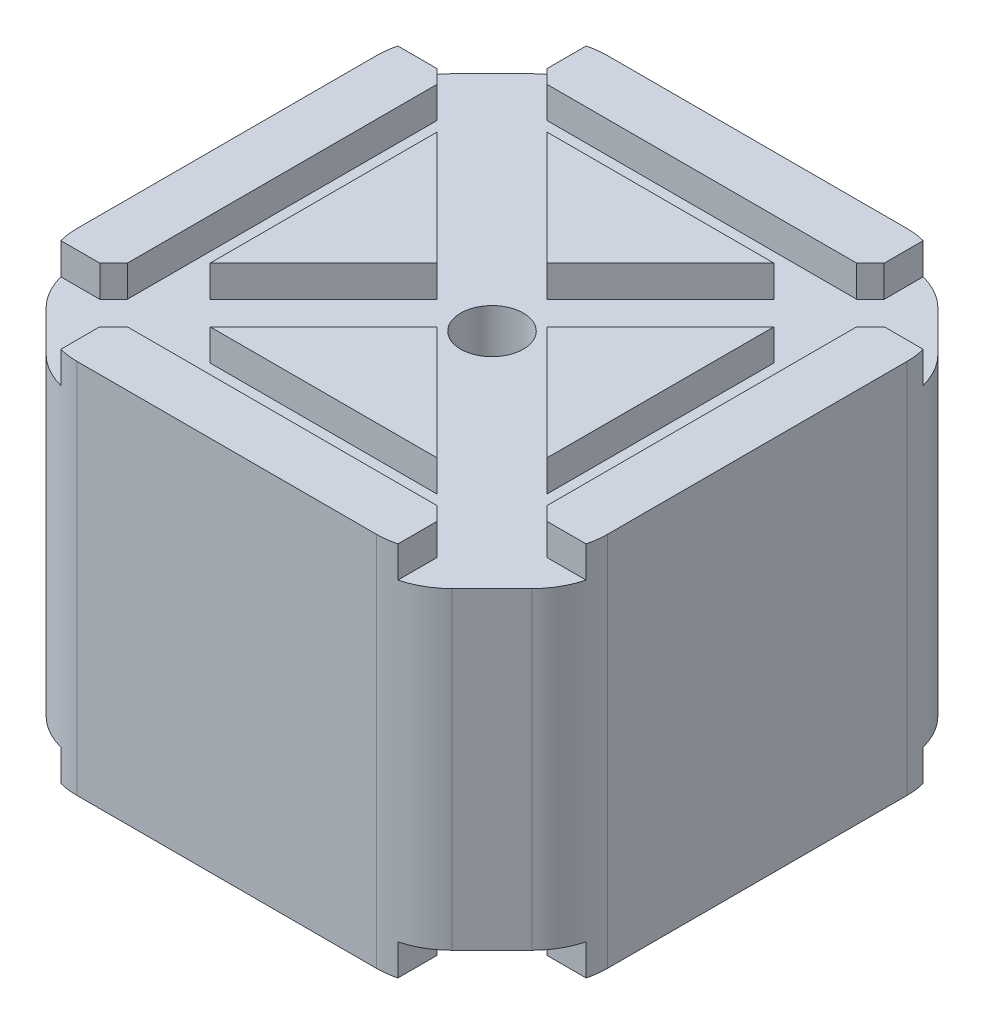
SolidWorks part; units mm, degrees
material "Alumina"
ref_plane "Front Plane" through (0, 0, 0) normal (0, 0, 1) x (1, 0, 0)
ref_plane "Top Plane" through (0, 0, 0) normal (0, 1, 0) x (1, 0, 0)
ref_plane "Right Plane" through (0, 0, 0) normal (1, 0, 0) x (0, 0, -1)
sketch "Sketch1" plane through (0, 0, 0) normal (0, 1, 0) x (1, 0, 0)
  line L0 (-21.15, 16.7509) -> (-16.7509, 21.15)
  line L1 (-16.7509, -21.15) -> (16.7509, -21.15)
  line L2 (-21.15, -16.7509) -> (-21.15, 16.7509)
  line L3 (-16.7509, 21.15) -> (16.7509, 21.15)
  line L4 (21.15, -16.7509) -> (21.15, 16.7509)
  line L7 (16.7509, 21.15) -> (21.15, 16.7509)
  line L8 (16.7509, -21.15) -> (21.15, -16.7509)
  line L9 (-21.15, -16.7509) -> (-16.7509, -21.15)
  point P0 (0, 0)
  dimension "D1" = 42.3
  dimension "D2" = 42.3
  dimension "D3" = 53.6
  dimension "D4" = 45
  dimension "D5" = 45
  dimension "D7" = 53.6
extrude "Boss-Extrude1" add sketch "Sketch1" along normal blind 15
sketch "Sketch18" plane through (0, 0, 21.15) normal (0, 0, 1) x (1, 0, 0)
  line L0 (13.4509, 15) -> (13.4509, 12.5)
  line L1 (-16.7509, 15) -> (16.7509, 15) construction
  line L2 (13.4509, 12.5) -> (16.7509, 12.5)
  line L3 (16.7509, 15) -> (16.7509, 0) construction
  line L4 (16.7509, 12.5) -> (16.7509, 15)
  line L5 (16.7509, 15) -> (13.4509, 15)
  line L6 (-13.4509, 15) -> (-13.4509, 12.5)
  line L7 (-13.4509, 12.5) -> (-16.7509, 12.5)
  line L8 (-16.7509, 15) -> (-16.7509, 0) construction
  line L9 (-16.7509, 12.5) -> (-16.7509, 15)
  line L10 (-16.7509, 15) -> (-13.4509, 15)
  dimension "D1" = 2.5
  dimension "D2" = 2.5
  dimension "D3" = 3.3
  dimension "D4" = 3.3
extrude "Cut-Extrude10" cut sketch "Sketch18" against normal through all
sketch "Sketch19" plane through (21.15, 0, 0) normal (1, 0, 0) x (0, 0, -1)
  line L0 (-13.4509, 15) -> (-13.4509, 12.5)
  line L1 (-16.7509, 15) -> (16.7509, 15) construction
  line L2 (-13.4509, 12.5) -> (-16.7509, 12.5)
  line L3 (-16.7509, 15) -> (-16.7509, 0) construction
  line L4 (-16.7509, 12.5) -> (-16.7509, 15)
  line L5 (-16.7509, 15) -> (-13.4509, 15)
  line L6 (13.4509, 15) -> (13.4509, 12.5)
  line L7 (13.4509, 12.5) -> (16.7509, 12.5)
  line L8 (16.7509, 15) -> (16.7509, 0) construction
  line L9 (16.7509, 12.5) -> (16.7509, 15)
  line L10 (16.7509, 15) -> (13.4509, 15)
  dimension "D1" = 3.3
  dimension "D2" = 3.3
  dimension "D3" = 2.5
  dimension "D4" = 2.5
extrude "Cut-Extrude11" cut sketch "Sketch19" against normal through all
sketch "Sketch20" plane through (18.9505, 0, 18.9505) normal (0.7071, 0, 0.7071) x (0.7071, 0, -0.7071)
  line L0 (-3.1106, 12.5) -> (3.1106, 12.5)
  line L1 (3.1106, 12.5) -> (3.1106, 15)
  line L2 (3.1106, 15) -> (-3.1106, 15)
  line L3 (-3.1106, 15) -> (-3.1106, 12.5)
extrude "Cut-Extrude12" cut sketch "Sketch20" against normal through all
sketch "Sketch21" plane through (-18.9505, 0, 18.9505) normal (-0.7071, 0, 0.7071) x (0.7071, 0, 0.7071)
  line L0 (-3.1106, 12.5) -> (3.1106, 12.5)
  line L1 (3.1106, 12.5) -> (3.1106, 15)
  line L2 (3.1106, 15) -> (-3.1106, 15)
  line L3 (-3.1106, 15) -> (-3.1106, 12.5)
extrude "Cut-Extrude13" cut sketch "Sketch21" against normal through all
sketch "Sketch22" plane through (0, 12.5, 0) normal (0, 1, 0) x (1, 0, 0)
  circle A0 centre (0, 0) radius 2.5
  dimension "D1" = 5
extrude "Cut-Extrude14" cut sketch "Sketch22" against normal through all
mirror "Mirror1" about plane through (0, 0, 0) normal (0, -1, 0) of "Boss-Extrude1", "Cut-Extrude14", "Cut-Extrude13", "Cut-Extrude12", "Cut-Extrude11", "Cut-Extrude10"
sketch "Sketch23" plane through (0, 12.5, 0) normal (0, 1, 0) x (1, 0, 0)
  line L0 (-21.15, -14.4325) -> (-14.4325, -21.15)
  line L1 (-14.4325, -21.15) -> (-16.7509, -21.15)
  line L2 (-16.7509, -21.15) -> (-21.15, -16.7509)
  line L3 (-21.15, -16.7509) -> (-21.15, -14.4325)
  line L4 (-21.15, 14.4325) -> (-14.4325, 21.15)
  line L5 (-14.4325, 21.15) -> (-16.7509, 21.15)
  line L6 (-16.7509, 21.15) -> (-21.15, 16.7509)
  line L7 (-21.15, 16.7509) -> (-21.15, 14.4325)
  line L8 (14.4325, 21.15) -> (21.15, 14.4325)
  line L9 (21.15, 14.4325) -> (21.15, 16.7509)
  line L10 (21.15, 16.7509) -> (16.7509, 21.15)
  line L11 (16.7509, 21.15) -> (14.4325, 21.15)
  line L12 (14.4325, -21.15) -> (21.15, -14.4325)
  line L13 (21.15, -14.4325) -> (21.15, -16.7509)
  line L14 (21.15, -16.7509) -> (16.7509, -21.15)
  line L15 (16.7509, -21.15) -> (14.4325, -21.15)
  dimension "D1" = 9.5
  dimension "D2" = 9.5
  dimension "D3" = 9.5
  dimension "D4" = 9.5
extrude "Cut-Extrude15" cut sketch "Sketch23" against normal through all
fillet "Fillet8" radius 6 8 edges at (14.4325, 0, -21.15) (21.15, 0, -14.4325) (-21.15, 0, -14.4325) (-14.4325, 0, -21.15) (-14.4325, 0, 21.15) (-21.15, 0, 14.4325) (21.15, 0, 14.4325) (14.4325, 0, 21.15)
